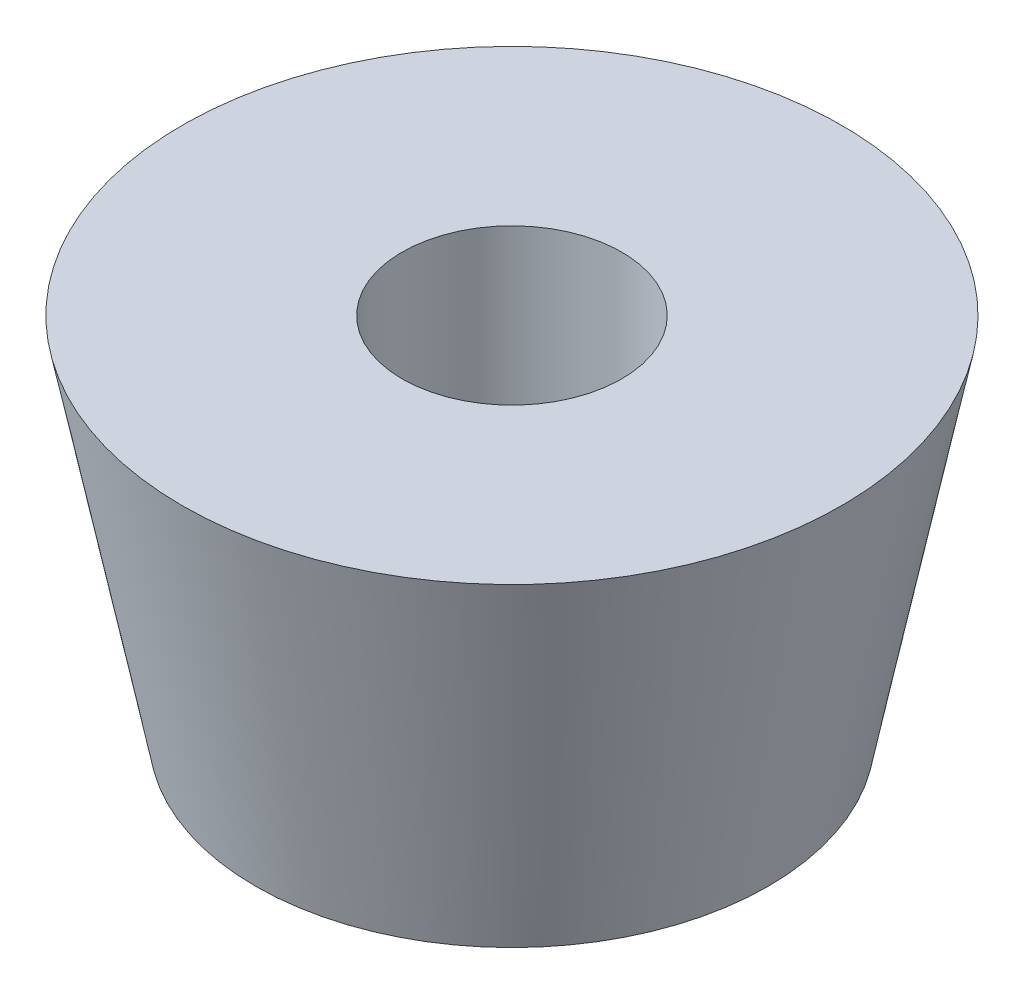
SolidWorks part; units mm, degrees
ref_plane "Front Plane" through (0, 0, 0) normal (0, 0, 1) x (1, 0, 0)
ref_plane "Top Plane" through (0, 0, 0) normal (0, 1, 0) x (1, 0, 0)
ref_plane "Right Plane" through (0, 0, 0) normal (1, 0, 0) x (0, 0, -1)
sketch "Sketch1" plane through (0, 0, 0) normal (1, 0, 0) x (0, 0, -1)
  line L0 (1.5, 0) -> (1.5, -5)
  line L1 (1.5, -5) -> (3.5, -5)
  line L2 (3.5, -5) -> (4.5, 0)
  line L3 (4.5, 0) -> (1.5, 0)
  line L4 (0, 0) -> (0, -5) construction
  dimension "D1" = 5
  dimension "D2" = 3
  dimension "D3" = 2
  dimension "D4" = 1.5
revolve "Revolve1" add sketch "Sketch1" angle 360 about L4
